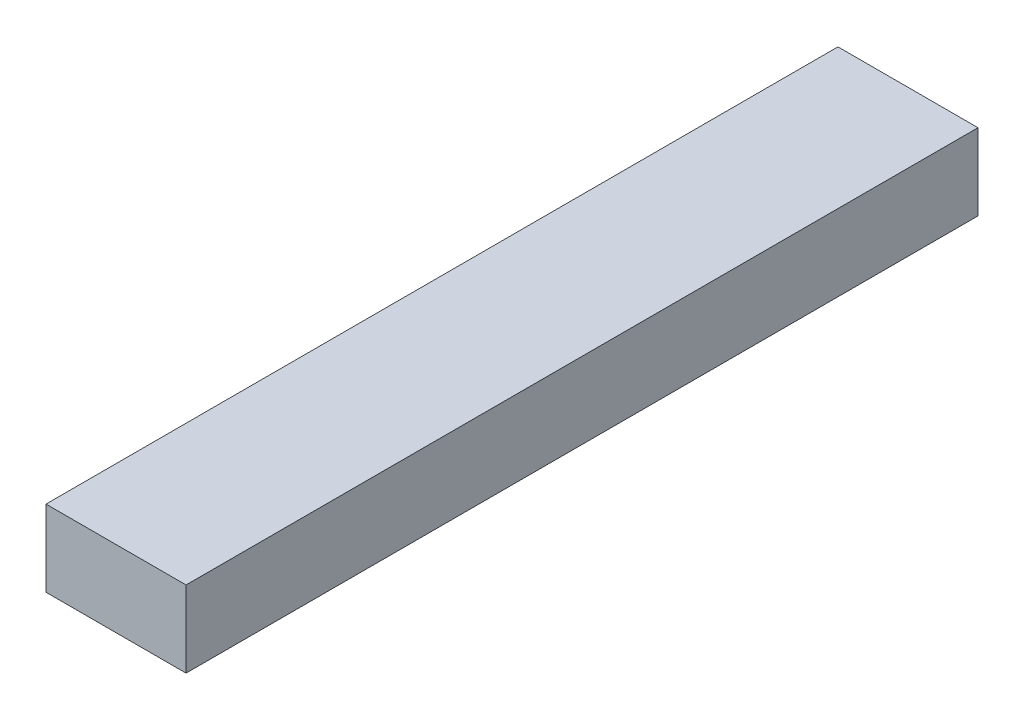
SolidWorks part; units mm, degrees
material "Простая углеродистая сталь"
ref_plane "Спереди" through (0, 0, 0) normal (0, 0, 1) x (1, 0, 0)
ref_plane "Сверху" through (0, 0, 0) normal (0, 1, 0) x (1, 0, 0)
ref_plane "Справа" through (0, 0, 0) normal (1, 0, 0) x (0, 0, -1)
sketch "Эскиз1" plane through (0, 0, 0) normal (0, 1, 0) x (1, 0, 0)
  line L1 (0, 0) -> (55, 0)
  line L2 (0, 0) -> (0, 311)
  line L3 (0, 311) -> (55, 311)
  line L4 (55, 0) -> (55, 311)
extrude "Бобышка-Вытянуть1" add sketch "Эскиз1" along normal blind 30
